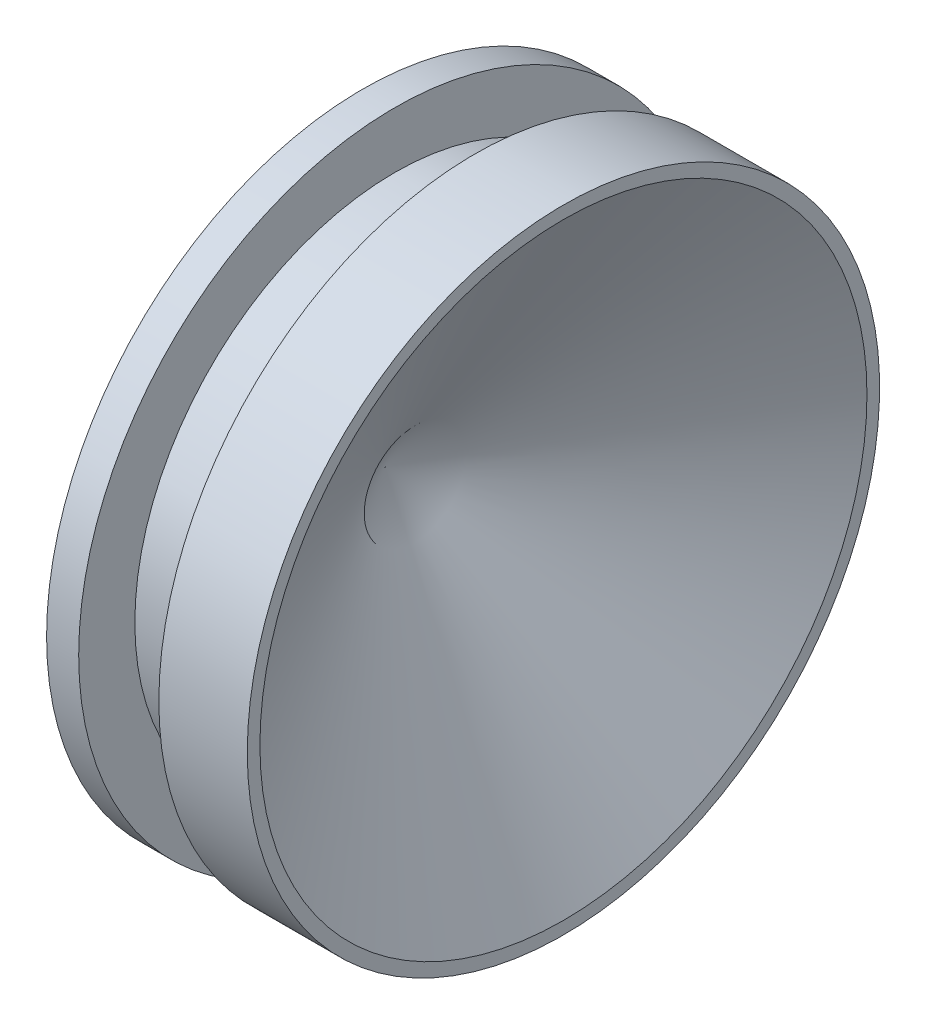
SolidWorks part; units mm, degrees
ref_plane "Front Plane" through (0, 0, 0) normal (0, 0, 1) x (1, 0, 0)
ref_plane "Top Plane" through (0, 0, 0) normal (0, 1, 0) x (1, 0, 0)
ref_plane "Right Plane" through (0, 0, 0) normal (1, 0, 0) x (0, 0, -1)
sketch "Sketch2" plane through (0, 0, 0) normal (0, 0, 1) x (1, 0, 0)
  line L0 (0, 0) -> (0, -2.5019)
  line L1 (0, -2.5019) -> (0.254, -2.5019)
  line L2 (0.254, -2.5019) -> (0.254, -2.0574)
  line L3 (0.254, -2.0574) -> (0.889, -2.0574)
  line L4 (0.889, -2.0574) -> (0.889, -2.5024)
  line L5 (0.889, -2.5024) -> (1.589, -2.5024)
  line L6 (0, 0) -> (3.5286, 0) construction
  line L7 (0, 0) -> (0.1776, 0)
  line L8 (1.589, -2.5024) -> (1.589, -2.4024)
  line L9 (0.1776, 0) -> (1.589, -2.4024)
revolve "Revolve1" add sketch "Sketch2" angle 360 about L6
